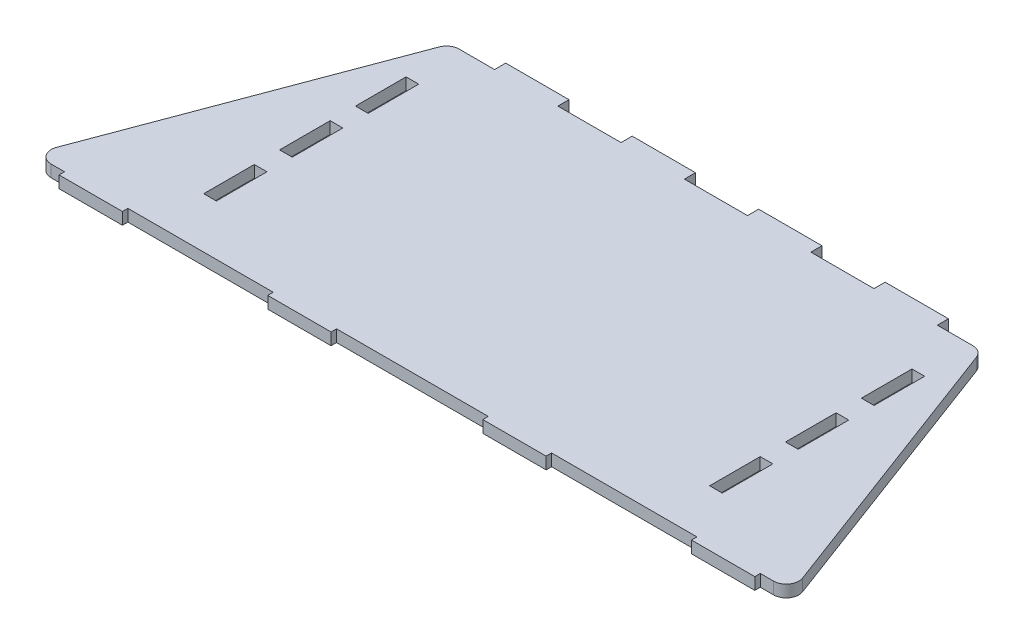
SolidWorks part; units mm, degrees
material "Balsa"
ref_plane "Front Plane" through (0, 0, 0) normal (0, 0, 1) x (1, 0, 0)
ref_plane "Top Plane" through (0, 0, 0) normal (0, 1, 0) x (1, 0, 0)
ref_plane "Right Plane" through (0, 0, 0) normal (1, 0, 0) x (0, 0, -1)
sketch "Sketch1" plane through (0, 0, 0) normal (0, 1, 0) x (1, 0, 0)
  line L0 (-190.5, -76.2) -> (190.5, -76.2)
  line L1 (190.5, -76.2) -> (133.35, 76.2)
  line L2 (133.35, 76.2) -> (-133.35, 76.2)
  line L3 (-133.35, 76.2) -> (-190.5, -76.2)
  point P4 (-161.925, 0)
  point P6 (0, 76.2)
  point P7 (0, -76.2)
  dimension "D1" = 381
  dimension "D2" = 266.7
  dimension "D3" = 152.4
extrude "Boss-Extrude1" add sketch "Sketch1" along normal blind 6
sketch "Sketch2" plane through (0, 6, 0) normal (0, 1, 0) x (1, 0, 0)
  line L0 (0, 76.2) -> (0, -76.2) construction
  line L1 (133.35, 76.2) -> (-133.35, 76.2) construction
  line L2 (-190.5, -76.2) -> (190.5, -76.2) construction
  line L3 (111.1504, 76.2) -> (111.1504, 81.788)
  line L4 (-15.8496, 76.2) -> (-47.6504, 76.2)
  line L5 (-15.8496, 76.2) -> (-15.8496, 81.788)
  line L6 (-15.8496, 81.788) -> (-47.6504, 81.788)
  line L7 (-47.6504, 76.2) -> (-47.6504, 81.788)
  line L8 (-79.3496, 76.2) -> (-111.1504, 76.2)
  line L9 (-79.3496, 76.2) -> (-79.3496, 81.788)
  line L10 (-79.3496, 81.788) -> (-111.1504, 81.788)
  line L11 (-111.1504, 76.2) -> (-111.1504, 81.788)
  line L12 (79.3496, 81.788) -> (111.1504, 81.788)
  line L13 (79.3496, 76.2) -> (79.3496, 81.788)
  line L14 (79.3496, 76.2) -> (111.1504, 76.2)
  line L15 (47.6504, 76.2) -> (47.6504, 81.788)
  line L16 (15.8496, 81.788) -> (47.6504, 81.788)
  line L17 (15.8496, 76.2) -> (15.8496, 81.788)
  line L18 (15.8496, 76.2) -> (47.6504, 76.2)
  line L19 (-161.925, 0) -> (161.925, 0) construction
  line L20 (-133.35, 76.2) -> (-190.5, -76.2) construction
  line L21 (190.5, -76.2) -> (133.35, 76.2) construction
  line L46 (69.8754, -76.2) -> (69.8754, -78.9432)
  line L47 (-69.8754, -76.2) -> (-38.0746, -76.2)
  line L48 (-69.8754, -76.2) -> (-69.8754, -78.9432)
  line L49 (-69.8754, -78.9432) -> (-38.0746, -78.9432)
  line L50 (-38.0746, -76.2) -> (-38.0746, -78.9432)
  line L51 (-174.6504, -76.2) -> (-142.8496, -76.2)
  line L52 (-174.6504, -76.2) -> (-174.6504, -78.9432)
  line L53 (-174.6504, -78.9432) -> (-142.8496, -78.9432)
  line L54 (-142.8496, -76.2) -> (-142.8496, -78.9432)
  line L55 (69.8754, -76.2) -> (38.0746, -76.2)
  line L56 (38.0746, -76.2) -> (38.0746, -78.9432)
  line L57 (69.8754, -78.9432) -> (38.0746, -78.9432)
  line L58 (174.6504, -76.2) -> (174.6504, -78.9432)
  line L59 (174.6504, -76.2) -> (142.8496, -76.2)
  line L60 (142.8496, -76.2) -> (142.8496, -78.9432)
  line L61 (174.6504, -78.9432) -> (142.8496, -78.9432)
  point P15 (-95.25, 81.788)
  point P16 (-31.75, 81.788)
  point P39 (-158.75, -78.9432)
  point P40 (-53.975, -78.9432)
  point P49 (53.975, -78.9432)
  dimension "D1" = 31.8008
  dimension "D2" = 63.5
  dimension "D3" = 63.5
  dimension "D4" = 5.588
  dimension "D6" = 2.7432
  dimension "D5" = 104.775
  dimension "D7" = 107.95
extrude "Tabs" add sketch "Sketch2" against normal up to surface (6 mm away) up to face at (0, 0, 0)
fillet "Fillet2" radius 6.35 2 edges at (190.5, 3, 76.2) (-190.5, 3, 76.2)
fillet "Fillet3" radius 6.35 2 edges at (-133.35, 3, -76.2) (133.35, 3, -76.2)
sketch "Sketch5" plane through (0, 6, 0) normal (0, 1, 0) x (1, 0, 0)
  line L0 (0, 76.2) -> (0, -76.2) construction
  line L1 (15.8496, 76.2) -> (-15.8496, 76.2) construction
  line L3 (-161.925, 0) -> (161.925, 0) construction
  line L4 (187.2826, -67.6204) -> (134.8951, 72.0796) construction
  line L5 (-134.8951, 72.0796) -> (-187.2826, -67.6204) construction
  line L6 (123.825, -50.8) -> (123.825, -25.4)
  line L7 (130.175, 50.8) -> (123.825, 50.8)
  line L8 (130.175, 50.8) -> (130.175, 25.4)
  line L9 (130.175, 25.4) -> (123.825, 25.4)
  line L10 (123.825, 50.8) -> (123.825, 25.4)
  line L11 (130.175, 12.7) -> (123.825, 12.7)
  line L12 (130.175, 12.7) -> (130.175, -12.7)
  line L13 (130.175, -12.7) -> (123.825, -12.7)
  line L14 (123.825, 12.7) -> (123.825, -12.7)
  line L15 (130.175, -25.4) -> (123.825, -25.4)
  line L16 (130.175, -50.8) -> (130.175, -25.4)
  line L17 (130.175, -50.8) -> (123.825, -50.8)
  point P21 (130.175, 38.1)
  point P22 (130.175, 0)
  dimension "D1" = 25.4
  dimension "D2" = 38.1
  dimension "D3" = 6.35
extrude "Tab Cut Outs" cut sketch "Sketch5" against normal up to surface (6 mm away) up to face at (0, 0, -0.7606)
ref_plane "Plane1" through (0, 0, 0) normal (-1, 0, 0) x (0, 0, 1)
mirror "Mirror1" about plane through (0, 0, 0) normal (-1, 0, 0) of "Tab Cut Outs"
sketch "Sketch4" plane through (0, 6, 0) normal (0, 1, 0) x (1, 0, 0)
  line L0 (-130.175, 50.8) -> (-123.825, 50.8) construction
  line L1 (-123.825, 25.4) -> (-130.175, 25.4) construction
  line L2 (-130.175, 25.4) -> (-130.175, 50.8) construction
  line L3 (-123.825, 50.8) -> (-123.825, 25.4) construction
  line L4 (-123.825, -25.4) -> (-130.175, -25.4)
  line L5 (-123.825, -50.8) -> (-123.825, -25.4)
  line L6 (-130.175, -50.8) -> (-123.825, -50.8)
  line L7 (-130.175, -25.4) -> (-130.175, -50.8)
  line L8 (-123.825, -25.4) -> (-130.175, -25.4) construction
  line L9 (-123.825, -50.8) -> (-123.825, -25.4) construction
  line L10 (-130.175, -50.8) -> (-123.825, -50.8) construction
  line L11 (-130.175, -25.4) -> (-130.175, -50.8) construction
  line L12 (-123.825, -12.7) -> (-123.825, 12.7)
  line L13 (-130.175, -12.7) -> (-123.825, -12.7)
  line L14 (-130.175, 12.7) -> (-130.175, -12.7)
  line L15 (-123.825, 12.7) -> (-130.175, 12.7)
  line L16 (-123.825, -12.7) -> (-123.825, 12.7) construction
  line L17 (-130.175, -12.7) -> (-123.825, -12.7) construction
  line L18 (-130.175, 12.7) -> (-130.175, -12.7) construction
  line L19 (-123.825, 12.7) -> (-130.175, 12.7) construction
  line L20 (-130.175, 50.8) -> (-123.825, 50.8) construction
  line L21 (-123.825, 25.4) -> (-130.175, 25.4) construction
  line L22 (-130.175, 25.4) -> (-130.175, 50.8) construction
  line L23 (-123.825, 50.8) -> (-123.825, 25.4) construction
  line L24 (-123.9266, -25.5016) -> (-130.0734, -25.5016)
  line L25 (-130.0734, -25.5016) -> (-130.0734, -50.6984)
  line L26 (-130.0734, -50.6984) -> (-123.9266, -50.6984)
  line L27 (-123.9266, -50.6984) -> (-123.9266, -25.5016)
  line L28 (-123.9266, -12.5984) -> (-123.9266, 12.5984)
  line L29 (-123.9266, 12.5984) -> (-130.0734, 12.5984)
  line L30 (-130.0734, 12.5984) -> (-130.0734, -12.5984)
  line L31 (-130.0734, -12.5984) -> (-123.9266, -12.5984)
  line L32 (-130.0734, 50.6984) -> (-123.9266, 50.6984)
  line L33 (-123.9266, 50.6984) -> (-123.9266, 25.5016)
  line L34 (-123.9266, 25.5016) -> (-130.0734, 25.5016)
  line L35 (-130.0734, 25.5016) -> (-130.0734, 50.6984)
  line L36 (-174.752, -79.0448) -> (-142.748, -79.0448)
  line L37 (-174.752, -79.0448) -> (-142.748, -79.0448)
  line L38 (-69.977, -79.0448) -> (-37.973, -79.0448)
  line L39 (-69.977, -79.0448) -> (-37.973, -79.0448)
  line L40 (-37.973, -79.0448) -> (-37.973, -76.3016)
  line L41 (-37.973, -79.0448) -> (-37.973, -76.3016)
  line L42 (-37.973, -76.3016) -> (37.973, -76.3016)
  line L43 (-37.973, -76.3016) -> (37.973, -76.3016)
  line L44 (37.973, -76.3016) -> (37.973, -79.0448)
  line L45 (37.973, -76.3016) -> (37.973, -79.0448)
  line L46 (37.973, -79.0448) -> (69.977, -79.0448)
  line L47 (37.973, -79.0448) -> (69.977, -79.0448)
  line L48 (69.977, -79.0448) -> (69.977, -76.3016)
  line L49 (69.977, -79.0448) -> (69.977, -76.3016)
  line L50 (69.977, -76.3016) -> (142.748, -76.3016)
  line L51 (69.977, -76.3016) -> (142.748, -76.3016)
  line L52 (142.748, -76.3016) -> (142.748, -79.0448)
  line L53 (142.748, -76.3016) -> (142.748, -79.0448)
  line L54 (142.748, -79.0448) -> (174.752, -79.0448)
  line L55 (142.748, -79.0448) -> (174.752, -79.0448)
  line L56 (174.752, -79.0448) -> (174.752, -76.3016)
  line L57 (174.752, -79.0448) -> (174.752, -76.3016)
  line L59 (130.0734, 25.5016) -> (130.0734, 50.6984)
  line L60 (123.9266, 25.5016) -> (130.0734, 25.5016)
  line L61 (123.9266, 50.6984) -> (123.9266, 25.5016)
  line L62 (130.0734, 50.6984) -> (123.9266, 50.6984)
  line L63 (130.0734, 25.5016) -> (130.0734, 50.6984)
  line L64 (123.9266, 25.5016) -> (130.0734, 25.5016)
  line L65 (123.9266, 50.6984) -> (123.9266, 25.5016)
  line L66 (130.0734, 50.6984) -> (123.9266, 50.6984)
  line L79 (130.0734, -12.5984) -> (130.0734, 12.5984)
  line L80 (123.9266, -12.5984) -> (130.0734, -12.5984)
  line L81 (123.9266, 12.5984) -> (123.9266, -12.5984)
  line L82 (130.0734, 12.5984) -> (123.9266, 12.5984)
  line L83 (130.0734, -12.5984) -> (130.0734, 12.5984)
  line L84 (123.9266, -12.5984) -> (130.0734, -12.5984)
  line L85 (123.9266, 12.5984) -> (123.9266, -12.5984)
  line L86 (130.0734, 12.5984) -> (123.9266, 12.5984)
  line L88 (174.752, -76.3016) -> (181.3369, -76.3016)
  line L89 (187.3778, -67.5847) -> (134.9903, 72.1153)
  line L90 (128.9494, 76.3016) -> (111.252, 76.3016)
  line L91 (111.252, 76.3016) -> (111.252, 81.8896)
  line L92 (111.252, 76.3016) -> (111.252, 81.8896)
  line L93 (111.252, 81.8896) -> (79.248, 81.8896)
  line L94 (111.252, 81.8896) -> (79.248, 81.8896)
  line L95 (79.248, 81.8896) -> (79.248, 76.3016)
  line L96 (79.248, 81.8896) -> (79.248, 76.3016)
  line L97 (79.248, 76.3016) -> (47.752, 76.3016)
  line L98 (79.248, 76.3016) -> (47.752, 76.3016)
  line L99 (47.752, 76.3016) -> (47.752, 81.8896)
  line L100 (47.752, 76.3016) -> (47.752, 81.8896)
  line L101 (47.752, 81.8896) -> (15.748, 81.8896)
  line L102 (47.752, 81.8896) -> (15.748, 81.8896)
  line L103 (15.748, 81.8896) -> (15.748, 76.3016)
  line L104 (15.748, 81.8896) -> (15.748, 76.3016)
  line L105 (15.748, 76.3016) -> (-15.748, 76.3016)
  line L106 (15.748, 76.3016) -> (-15.748, 76.3016)
  line L107 (-134.9903, 72.1153) -> (-187.3778, -67.5847)
  line L108 (-15.748, 76.3016) -> (-15.748, 81.8896)
  line L109 (-15.748, 76.3016) -> (-15.748, 81.8896)
  line L110 (-15.748, 81.8896) -> (-47.752, 81.8896)
  line L111 (-15.748, 81.8896) -> (-47.752, 81.8896)
  line L112 (-47.752, 81.8896) -> (-47.752, 76.3016)
  line L113 (-47.752, 81.8896) -> (-47.752, 76.3016)
  line L114 (-47.752, 76.3016) -> (-79.248, 76.3016)
  line L115 (-47.752, 76.3016) -> (-79.248, 76.3016)
  line L116 (-79.248, 76.3016) -> (-79.248, 81.8896)
  line L117 (-79.248, 76.3016) -> (-79.248, 81.8896)
  line L118 (-79.248, 81.8896) -> (-111.252, 81.8896)
  line L119 (-79.248, 81.8896) -> (-111.252, 81.8896)
  line L120 (-111.252, 81.8896) -> (-111.252, 76.3016)
  line L121 (-111.252, 81.8896) -> (-111.252, 76.3016)
  line L122 (-111.252, 76.3016) -> (-128.9494, 76.3016)
  line L123 (-111.252, 76.3016) -> (-128.9494, 76.3016)
  line L124 (-181.3369, -76.3016) -> (-174.752, -76.3016)
  line L126 (-181.3369, -76.3016) -> (-174.752, -76.3016)
  line L132 (174.752, -76.3016) -> (181.3369, -76.3016)
  line L133 (187.3778, -67.5847) -> (134.9903, 72.1153)
  line L134 (128.9494, 76.3016) -> (111.252, 76.3016)
  line L151 (-134.9903, 72.1153) -> (-187.3778, -67.5847)
  line L216 (-142.748, -76.3016) -> (-69.977, -76.3016)
  line L217 (-142.748, -76.3016) -> (-69.977, -76.3016)
  line L218 (-69.977, -76.3016) -> (-69.977, -79.0448)
  line L219 (-69.977, -76.3016) -> (-69.977, -79.0448)
  line L226 (-174.752, -76.3016) -> (-174.752, -79.0448)
  line L227 (-174.752, -76.3016) -> (-174.752, -79.0448)
  line L230 (-142.748, -79.0448) -> (-142.748, -76.3016)
  line L231 (-142.748, -79.0448) -> (-142.748, -76.3016)
  line L249 (130.0734, -50.6984) -> (130.0734, -25.5016)
  line L250 (123.9266, -50.6984) -> (130.0734, -50.6984)
  line L251 (123.9266, -25.5016) -> (123.9266, -50.6984)
  line L252 (130.0734, -25.5016) -> (123.9266, -25.5016)
  line L253 (130.0734, -50.6984) -> (130.0734, -25.5016)
  line L254 (123.9266, -50.6984) -> (130.0734, -50.6984)
  line L255 (123.9266, -25.5016) -> (123.9266, -50.6984)
  line L256 (130.0734, -25.5016) -> (123.9266, -25.5016)
  arc A4 (181.3369, -76.3016) -> (187.3778, -67.5847) centre (181.3369, -69.85) ccw
  arc A5 (-187.3778, -67.5847) -> (-181.3369, -76.3016) centre (-181.3369, -69.85) ccw
  arc A6 (181.3369, -76.3016) -> (187.3778, -67.5847) centre (181.3369, -69.85) ccw
  arc A7 (-187.3778, -67.5847) -> (-181.3369, -76.3016) centre (-181.3369, -69.85) ccw
  arc A8 (-128.9494, 76.3016) -> (-134.9903, 72.1153) centre (-128.9494, 69.85) ccw
  arc A9 (-128.9494, 76.3016) -> (-134.9903, 72.1153) centre (-128.9494, 69.85) ccw
  arc A10 (134.9903, 72.1153) -> (128.9494, 76.3016) centre (128.9494, 69.85) ccw
  arc A11 (134.9903, 72.1153) -> (128.9494, 76.3016) centre (128.9494, 69.85) ccw
  dimension "D1" = 0.1016
  dimension "D2" = 0.1016
  dimension "D3" = 0.1016
  dimension "D4" = 0.1016
  dimension "D5" = 0
  dimension "D6" = 0
  dimension "D7" = 0.1016
extrude "KERF" [suppressed] add sketch "Sketch4" against normal up to surface (6 mm away)
